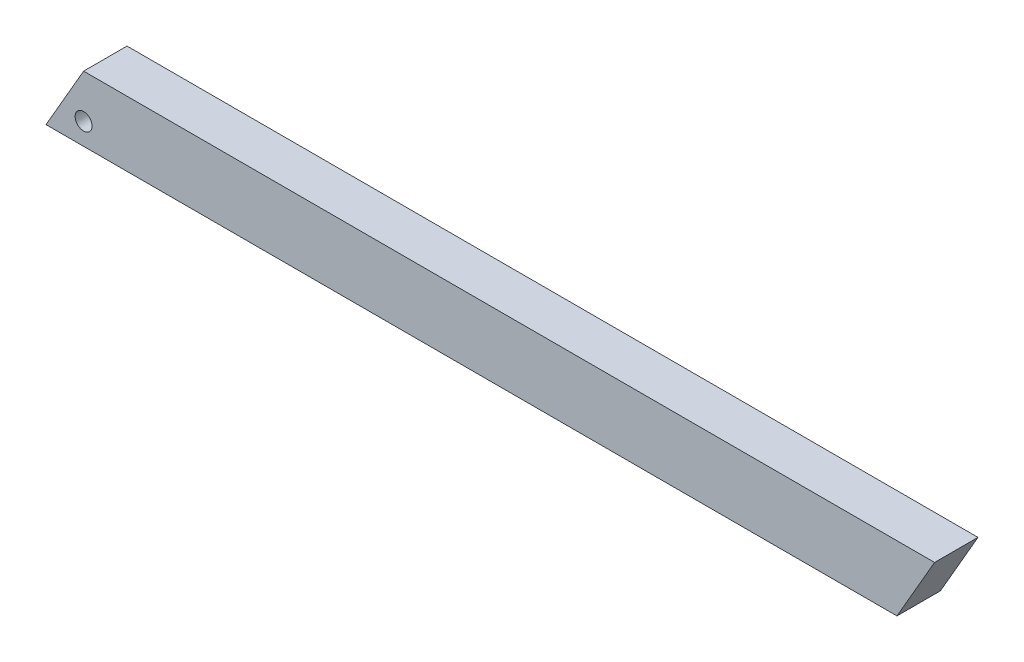
SolidWorks part; units mm, degrees
ref_plane "Front Plane" through (0, 0, 0) normal (0, 0, 1) x (1, 0, 0)
ref_plane "Top Plane" through (0, 0, 0) normal (0, 1, 0) x (1, 0, 0)
ref_plane "Right Plane" through (0, 0, 0) normal (1, 0, 0) x (0, 0, -1)
sketch "Sketch1" plane through (0, 0, 0) normal (0, 0, 1) x (1, 0, 0)
  line L0 (248.8682, 0) -> (237.8696, -19.05)
  line L1 (-248.8682, 19.05) -> (248.8682, 19.05) construction
  line L2 (-248.8682, 19.05) -> (-248.8682, -19.05) construction
  line L3 (-248.8682, -19.05) -> (248.8682, -19.05) construction
  line L4 (248.8682, 19.05) -> (248.8682, -19.05) construction
  line L5 (-248.8682, 19.05) -> (248.8682, -19.05) construction
  line L6 (-248.8682, -19.05) -> (248.8682, 19.05) construction
  line L7 (248.8682, 0) -> (259.8667, 19.05)
  line L8 (-248.8682, 0) -> (-237.8696, 19.05)
  line L9 (-248.8682, 0) -> (-259.8667, -19.05)
  line L10 (-259.8667, -19.05) -> (237.8696, -19.05)
  line L11 (-237.8696, 19.05) -> (259.8667, 19.05)
  circle A0 centre (-237.8696, -6.35) radius 4.9595
  point P0 (0, 0)
  dimension "D1" = 497.7363
  dimension "D2" = 38.1
  dimension "D3" = 12.7
  dimension "D4" = 12.7
extrude "Boss-Extrude1" add sketch "Sketch1" along normal blind 25.4
